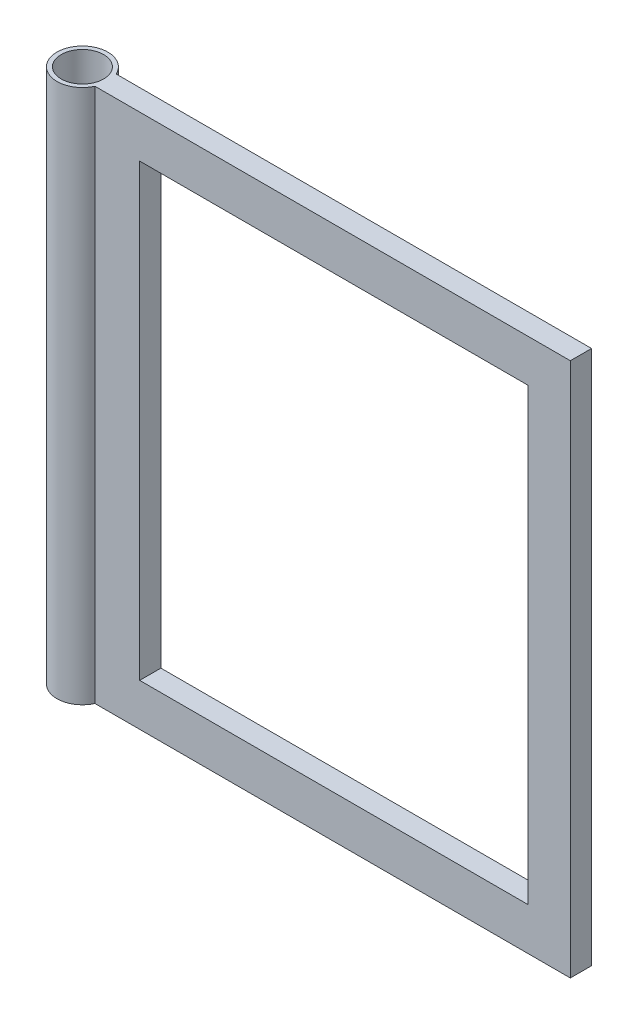
SolidWorks part; units mm, degrees
material "6063-O"
ref_plane "Front Plane" through (0, 0, 0) normal (0, 0, 1) x (1, 0, 0)
ref_plane "Top Plane" through (0, 0, 0) normal (0, 1, 0) x (1, 0, 0)
ref_plane "Right Plane" through (0, 0, 0) normal (1, 0, 0) x (0, 0, -1)
sketch "Sketch1" plane through (0, 0, 0) normal (0, 0, 1) x (1, 0, 0)
  line L0 (0, 0) -> (0, 1260) construction
  line L1 (-50, 0) -> (-50, 1260)
  line L2 (-50, 1260) -> (-60, 1260)
  line L3 (-60, 1260) -> (-60, 0)
  line L4 (-60, 0) -> (-50, 0)
  dimension "D1" = 1260
  dimension "D2" = 10
  dimension "D3" = 50
revolve "Revolve1" add sketch "Sketch1" angle 360 about L0
sketch "Sketch2" plane through (0, 0, 0) normal (0, 0, 1) x (1, 0, 0)
  line L0 (60, 1260) -> (1175, 1260)
  line L1 (1175, 1260) -> (1175, 0)
  line L2 (1175, 0) -> (60, 0)
  line L3 (60, 0) -> (60, 1260)
  line L4 (1075, 100) -> (160, 100)
  line L5 (160, 100) -> (160, 1160)
  line L6 (160, 1160) -> (1075, 1160)
  line L7 (1075, 1160) -> (1075, 100)
  dimension "D1" = 1115
  dimension "D2" = 100
extrude "Boss-Extrude1" add sketch "Sketch2" along normal mid plane 50 separate body
sketch "Sketch3" plane through (60, 0, 0) normal (-1, 0, 0) x (0, 0, 1)
  line L0 (25, 1260) -> (-25, 1260)
  line L1 (-25, 1260) -> (-25, 0)
  line L2 (-25, 0) -> (25, 0)
  line L3 (25, 0) -> (25, 1260)
extrude "Boss-Extrude2" add sketch "Sketch3" along normal up to next (10 mm away)
